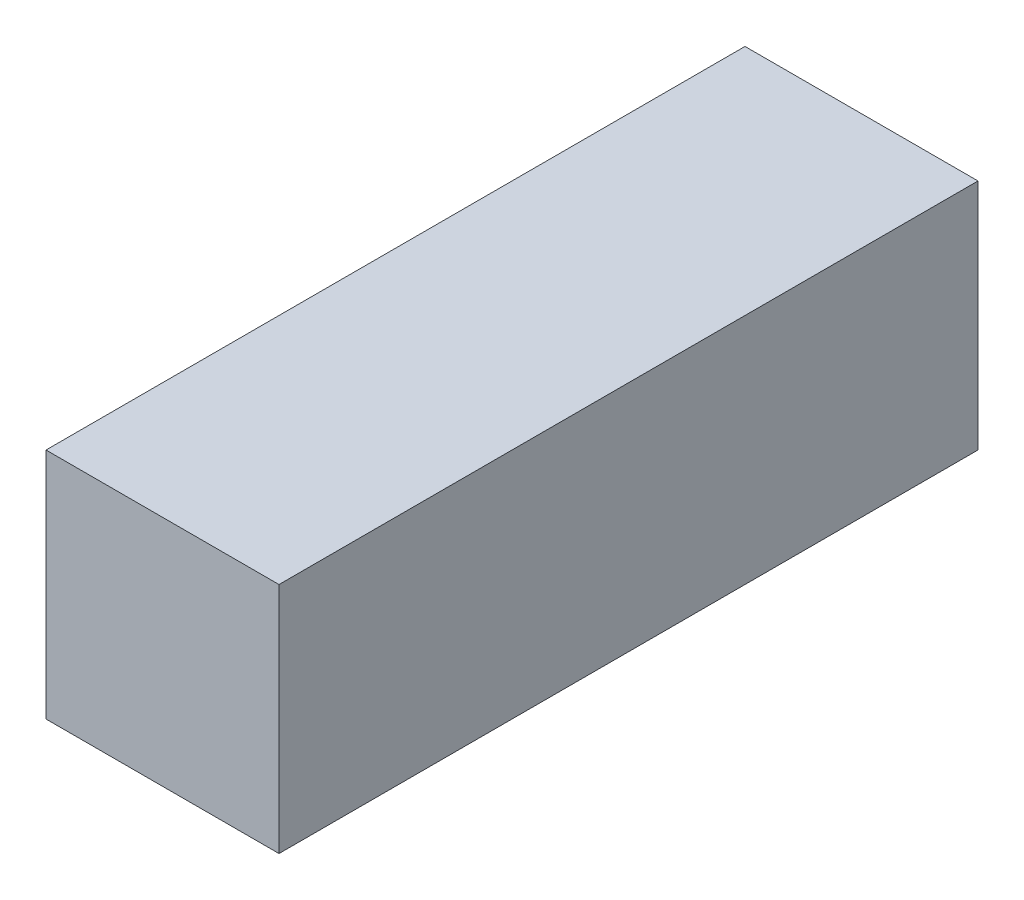
SolidWorks part; units mm, degrees
material "Brass"
ref_plane "Front Plane" through (0, 0, 0) normal (0, 0, 1) x (1, 0, 0)
ref_plane "Top Plane" through (0, 0, 0) normal (0, 1, 0) x (1, 0, 0)
ref_plane "Right Plane" through (0, 0, 0) normal (1, 0, 0) x (0, 0, -1)
sketch "Sketch1" plane through (0, 0, 0) normal (0, 0, 1) x (1, 0, 0)
  line L1 (-3.175, -3.175) -> (3.175, -3.175)
  line L2 (-3.175, -3.175) -> (-3.175, 3.175)
  line L3 (-3.175, 3.175) -> (3.175, 3.175)
  line L4 (3.175, -3.175) -> (3.175, 3.175)
  line L5 (-3.175, -3.175) -> (3.175, 3.175) construction
  line L6 (-3.175, 3.175) -> (3.175, -3.175) construction
  point P0 (0, 0)
  dimension "D1" = 6.35
extrude "Boss-Extrude1" add sketch "Sketch1" along normal blind 19.05
